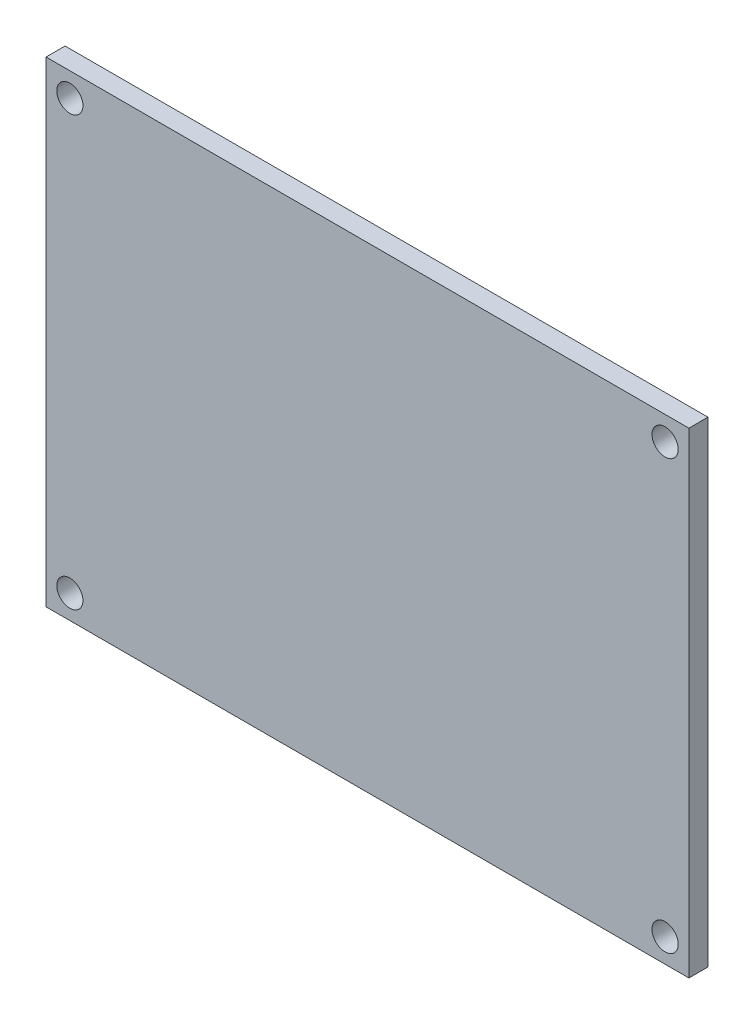
SolidWorks part; units mm, degrees
ref_plane "正面" through (0, 0, 0) normal (0, 0, 1) x (1, 0, 0)
ref_plane "平面" through (0, 0, 0) normal (0, 1, 0) x (1, 0, 0)
ref_plane "右側面" through (0, 0, 0) normal (1, 0, 0) x (0, 0, -1)
sketch "Model" plane through (0, 0, 0) normal (0, 0, 1) x (1, 0, 0)
  line L0 (0, 0) -> (54, 0)
  line L3 (54, 0) -> (54, 40)
  line L4 (54, 40) -> (0, 40)
  line L5 (0, 40) -> (0, 0)
  circle A0 centre (2, 2) radius 1.1
  circle A1 centre (52, 2) radius 1.1
  circle A2 centre (52, 38) radius 1.1
  circle A3 centre (2, 38) radius 1.1
  dimension "D3" = 2.2
  dimension "D1" = 40
  dimension "D2" = 54
extrude "ﾎﾞｽ - 押し出し1" add sketch "Model" along normal blind 1.6
